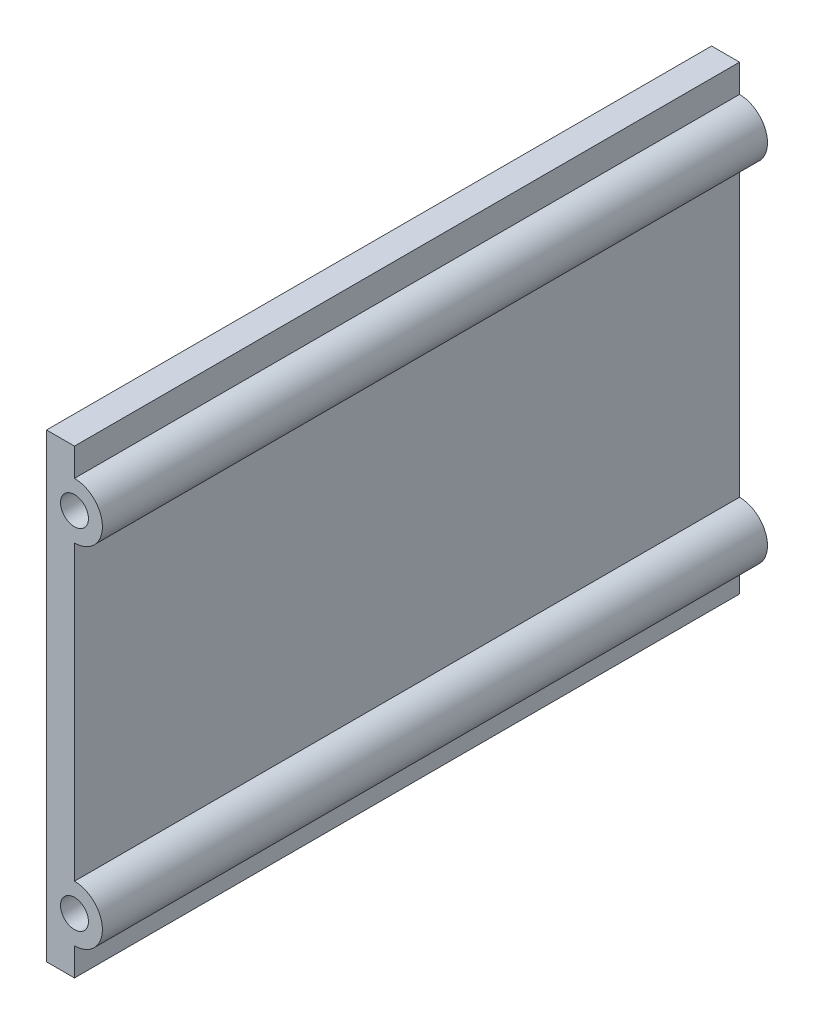
SolidWorks part; units mm, degrees
ref_plane "前视基准面" through (0, 0, 0) normal (0, 0, 1) x (1, 0, 0)
ref_plane "上视基准面" through (0, 0, 0) normal (0, 1, 0) x (1, 0, 0)
ref_plane "右视基准面" through (0, 0, 0) normal (1, 0, 0) x (0, 0, -1)
sketch "草图1" plane through (0, 0, 0) normal (0, 0, 1) x (1, 0, 0)
  line L3 (-166.5, 31.2106) -> (-166.5, -31.2106)
  line L4 (-161.5, 26.2106) -> (-161.5, -26.2106)
  line L6 (-166.5, 36.2106) -> (-166.5, 31.2106)
  line L7 (-166.5, -31.2106) -> (-166.5, -36.2106)
  line L9 (-161.5, 36.2106) -> (-161.5, 41.2106)
  line L10 (-161.5, 41.2106) -> (-166.5, 41.2106)
  line L11 (-166.5, 41.2106) -> (-166.5, 36.2106)
  line L12 (-161.5, -36.2106) -> (-161.5, -41.2106)
  line L13 (-161.5, -41.2106) -> (-166.5, -41.2106)
  line L14 (-166.5, -41.2106) -> (-166.5, -36.2106)
  arc A4 (-161.5, 26.2106) -> (-161.5, 36.2106) centre (-161.5, 31.2106) ccw
  arc A5 (-161.5, -36.2106) -> (-161.5, -26.2106) centre (-161.5, -31.2106) ccw
  circle A6 centre (-161.5, 31.2106) radius 2.5
  circle A7 centre (-161.5, -31.2106) radius 2.5
extrude "凸台-拉伸1" add sketch "草图1" along normal up to surface (119 mm away)
ref_plane "基准面1" through (0, 0, 0) normal (0, 1, 0) x (1, 0, 0)
ref_plane "基准面2" through (0, 37.5, 0) normal (0, 1, 0) x (1, 0, 0)
ref_plane "基准面3" through (0, -37.5, 0) normal (0, 1, 0) x (1, 0, 0)
ref_plane "基准面4" through (0, 0, 59.5) normal (0, 0, -1) x (-1, 0, 0)
ref_plane "基准面5" through (0, 0, 9.5) normal (0, 0, -1) x (-1, 0, 0)
ref_plane "基准面6" through (0, 0, 109.5) normal (0, 0, -1) x (-1, 0, 0)
